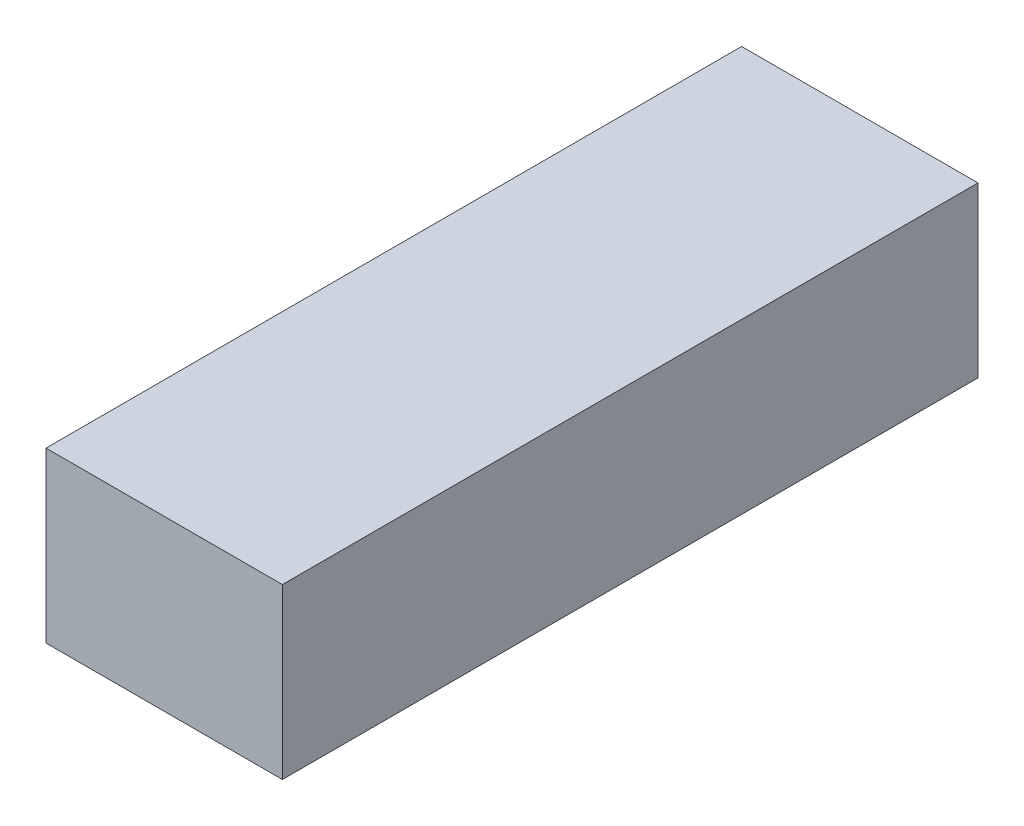
SolidWorks part; units mm, degrees
ref_plane "前视基准面" through (0, 0, 0) normal (0, 0, 1) x (1, 0, 0)
ref_plane "上视基准面" through (0, 0, 0) normal (0, 1, 0) x (1, 0, 0)
ref_plane "右视基准面" through (0, 0, 0) normal (1, 0, 0) x (0, 0, -1)
other "Configuration Table"
sketch "草图1" plane through (0, 0, 0) normal (0, 0, 1) x (1, 0, 0)
  line L1 (0, 0) -> (35, 0)
  line L2 (0, 0) -> (0, 25)
  line L3 (0, 25) -> (35, 25)
  line L4 (35, 0) -> (35, 25)
  dimension "D1" = 35
  dimension "D2" = 25
extrude "凸台-拉伸1" add sketch "草图1" along normal blind 103
